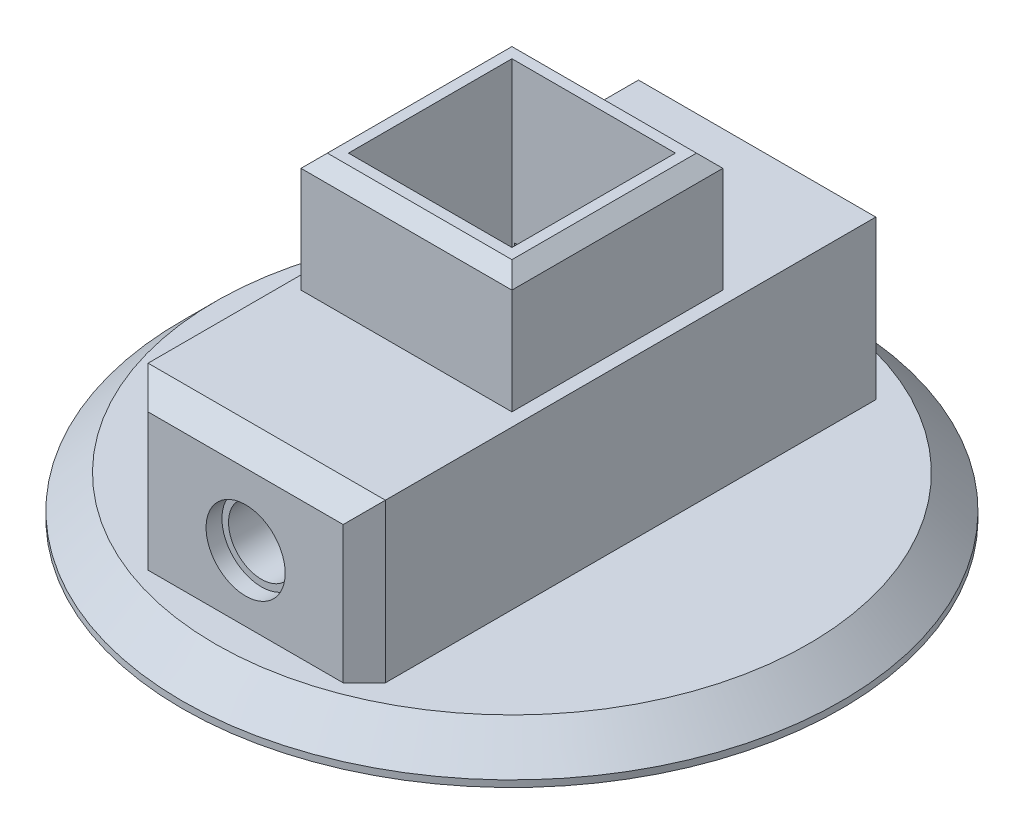
SolidWorks part; units mm, degrees
ref_plane "Front Plane" through (0, 0, 0) normal (0, 0, 1) x (1, 0, 0)
ref_plane "Top Plane" through (0, 0, 0) normal (0, 1, 0) x (1, 0, 0)
ref_plane "Right Plane" through (0, 0, 0) normal (1, 0, 0) x (0, 0, -1)
sketch "Sketch1" plane through (0, 0, 0) normal (0, 1, 0) x (1, 0, 0)
  line L0 (0, 16) -> (0, 0) construction
  line L1 (-8, 16) -> (8, 16)
  line L2 (-8, 16) -> (-8, 0)
  line L10 (8, 16) -> (8, 0)
  line L11 (-8, 0) -> (8, 0)
  dimension "D1" = 16
  dimension "D2" = 16
extrude "Boss-Extrude1" add sketch "Sketch1" along normal blind 24
sketch "Sketch12" plane through (0, 24, 0) normal (0, 1, 0) x (1, 0, 0)
  line L1 (-6.2, 14.2) -> (6.2, 14.2)
  line L2 (-6.2, 14.2) -> (-6.2, 1.8)
  line L3 (-6.2, 1.8) -> (6.2, 1.8)
  line L4 (6.2, 14.2) -> (6.2, 1.8)
  line L5 (0, 0) -> (0, 16) construction
  line L6 (8, 8) -> (-13.65, 8) construction
  line L7 (8, 16) -> (8, 0) construction
  dimension "D1" = 12.4
  dimension "D2" = 12.4
extrude "Cut-Extrude6" cut sketch "Sketch12" against normal offset from surface (22 mm away) 2 up to face at (0, 0, -8)
sketch "Sketch13" plane through (0, 0, 0) normal (0, 1, 0) x (1, 0, 0)
  line L0 (0, 16) -> (0, 0) construction
  circle A0 centre (0, 8) radius 25
  dimension "D1" = 50
extrude "Boss-Extrude2" add sketch "Sketch13" along normal blind 3
chamfer "Chamfer1" distance 2.5 angle 45 1 edges at (0, 3, 17)
sketch "Sketch14" plane through (0, 3, 0) normal (0, 1, 0) x (1, 0, 0)
  line L1 (-8, 16) -> (8, 16)
  line L5 (-8, 0) -> (8, 0)
  line L9 (0, 0) -> (0, 24.5816) construction
  line L11 (-8, 16) -> (-8, 0)
  line L13 (-9, 28.2) -> (-9, -12.2)
  line L16 (9, 28.2) -> (9, -12.2)
  line L17 (8, 16) -> (8, 0) construction
  line L18 (8, 16) -> (8, 0)
  line L19 (-9, 28.2) -> (9, 28.2)
  line L20 (-6.2, 14.2) -> (6.2, 14.2) construction
  line L21 (-9, -12.2) -> (9, -12.2)
  line L22 (-6.2, 1.8) -> (6.2, 1.8) construction
  dimension "D1" = 14
  dimension "D2" = 14
  dimension "D3" = 1
extrude "Boss-Extrude3" add sketch "Sketch14" along normal blind 12
chamfer "Chamfer2" distance 1.6 angle 45 6 edges at (-9, 9, 12.2) (9, 9, 12.2) (0, 15, 12.2) (-9, 9, -28.2) (0, 15, -28.2) (9, 9, -28.2)
chamfer "Chamfer5" distance 1 angle 45 4 edges at (0, 24, 0) (-8, 24, -8) (0, 24, -16) (8, 24, -8)
sketch "Sketch16" plane through (0, 0, -28.2) normal (0, 0, -1) x (-1, 0, 0)
  line L0 (0, 13) -> (0, -0.2824) construction
  line L1 (-6, 12) -> (6, 12)
  line L2 (-6, 12) -> (-6, 4)
  line L3 (-6, 4) -> (6, 4)
  line L4 (6, 12) -> (6, 4)
  line L6 (-6, 8) -> (6, 8) construction
  line L7 (8, 0) -> (-8, 0) construction
  dimension "D1" = 12
  dimension "D2" = 8
  dimension "D3" = 8
extrude "Cut-Extrude8" cut sketch "Sketch16" against normal blind 14
sketch "Sketch15" plane through (0, 0, -1.8) normal (0, 0, -1) x (-1, 0, 0)
  line L1 (6, 8) -> (-6, 8) construction
  line L2 (6, 4) -> (6, 12) construction
  line L3 (-6, 12) -> (-6, 4) construction
  circle A0 centre (0, 8) radius 1.3
  dimension "D1" = 2.6
extrude "Cut-Extrude7" cut sketch "Sketch15" against normal through all
sketch "Sketch17" plane through (0, 0, 12.2) normal (0, 0, 1) x (1, 0, 0)
  circle A0 centre (0, 8) radius 2.5
  dimension "D1" = 5
extrude "Cut-Extrude9" cut sketch "Sketch17" against normal blind 9
sketch "Sketch19" plane through (0, 0, 12.2) normal (0, 0, 1) x (1, 0, 0)
  circle A0 centre (0, 8) radius 3
  dimension "D1" = 6
extrude "Cut-Extrude10" cut sketch "Sketch19" against normal blind 1.2
sketch "Sketch18" plane through (0, 0, 0) normal (0, 1, 0) x (1, 0, 0)
  line L1 (0.25, -11) -> (-0.25, -11)
  line L2 (0.25, -11) -> (0.25, -8)
  line L3 (0.25, -8) -> (-0.25, -8)
  line L4 (-0.25, -11) -> (-0.25, -8)
  line L5 (0, -3.2) -> (0, -9.9382) construction
  line L6 (-2.5, -3.2) -> (2.5, -3.2) construction
  line L7 (-3, -11) -> (3, -11) construction
  point P4 (0.25, -11)
  point P11 (0, 0)
  dimension "D1" = 0.5
  dimension "D2" = 3
extrude "Boss-Extrude4" [suppressed] add sketch "Sketch18" along normal blind 5.65
chamfer "Chamfer6" [suppressed] distance 0.1 angle 45
